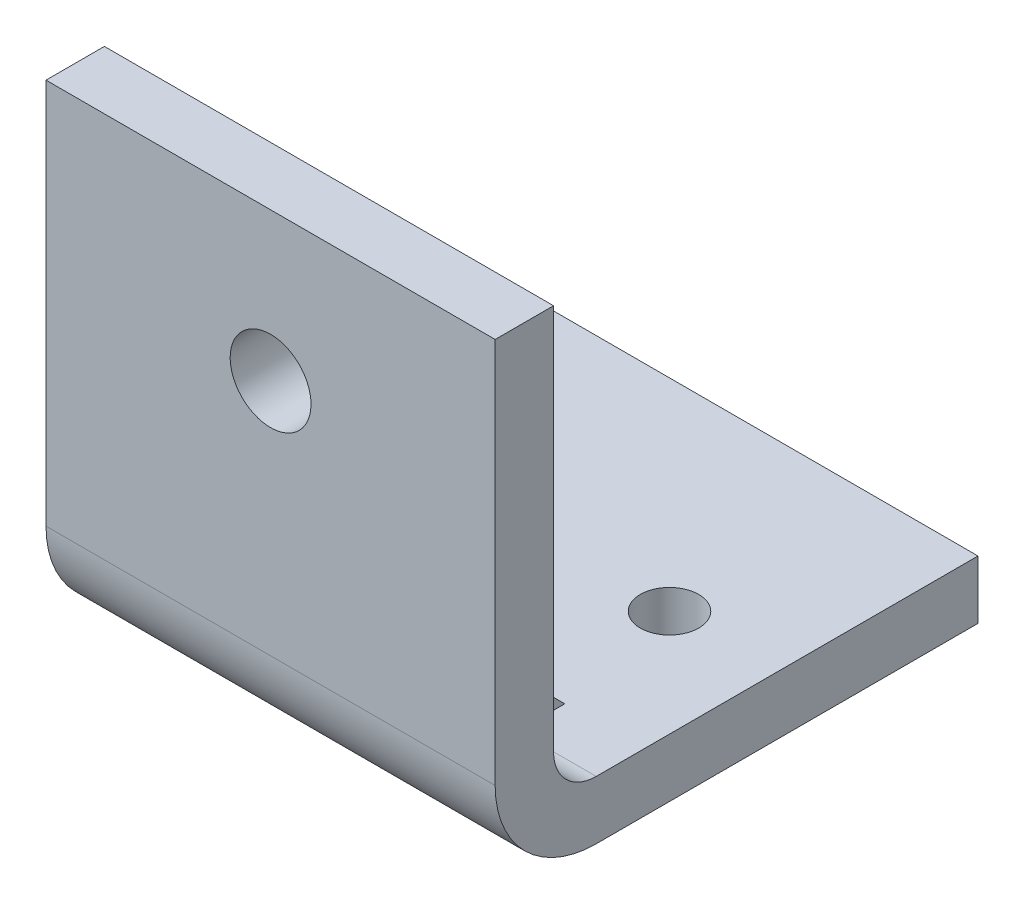
SolidWorks part; units mm, degrees
ref_plane "Piano frontale" through (0, 0, 0) normal (0, 0, 1) x (1, 0, 0)
ref_plane "Piano superiore" through (0, 0, 0) normal (0, 1, 0) x (1, 0, 0)
ref_plane "Piano destro" through (0, 0, 0) normal (1, 0, 0) x (0, 0, -1)
sketch "Schizzo1" plane through (0, 0, 0) normal (1, 0, 0) x (0, 0, -1)
  line L0 (0, 102) -> (0, 16)
  line L1 (16, 0) -> (101, 0)
  arc A0 (16, 0) -> (0, 16) centre (16, 16) cw
  point P6 (0, 0)
  dimension "D3" = 16
  dimension "D1" = 101
  dimension "D2" = 102
extrude "Estrusione-Sottile1" add sketch "Schizzo1" along normal mid plane 100 thin thin type mid plane wall 13
sketch "Schizzo2" plane through (0, 0, -6.5) normal (0, 0, -1) x (-1, 0, 0)
  line L0 (0, 102) -> (0, 0) construction
  line L1 (-50, 102) -> (50, 102) construction
  circle A0 centre (0, 69) radius 9
  dimension "D2" = 18
  dimension "D1" = 33
extrude "Taglio-Estrusione1" cut sketch "Schizzo2" against normal through all contours A0
sketch "Schizzo3" plane through (0, 6.5, 0) normal (0, 1, 0) x (1, 0, 0)
  line L0 (-50, 56) -> (50, 56) construction
  line L1 (-50, 16) -> (-50, 101) construction
  line L2 (50, 16) -> (50, 101) construction
  circle A0 centre (-23.6836, 56) radius 6.5
  circle A1 centre (26.3164, 56) radius 6.5
  dimension "D4" = 13
  dimension "D1" = 45
  dimension "D2" = 50
  dimension "D3" = 23.6836
extrude "Taglio-Estrusione2" cut sketch "Schizzo3" against normal through all contours A1 | A0
ref_plane "Piano1" through (30, 0, 0) normal (1, 0, 0) x (0, 0, -1)
sketch "Schizzo4" plane through (30, 0, 0) normal (1, 0, 0) x (0, 0, -1)
  line L0 (6.5, 26.5) -> (26.5, 6.5)
  line L1 (6.5, 102) -> (6.5, 16) construction
  line L2 (16, 6.5) -> (101, 6.5) construction
  dimension "D1" = 20
  dimension "D2" = 20
rib "Nervatura1" sketch "Schizzo4" sketch "Schizzo4" thickness 5 extrusion direction parallel to sketch draft on no parameters "D1"=5
mirror "Specchia1" about plane through (0, 0, 0) normal (1, 0, 0) of "Nervatura1"
